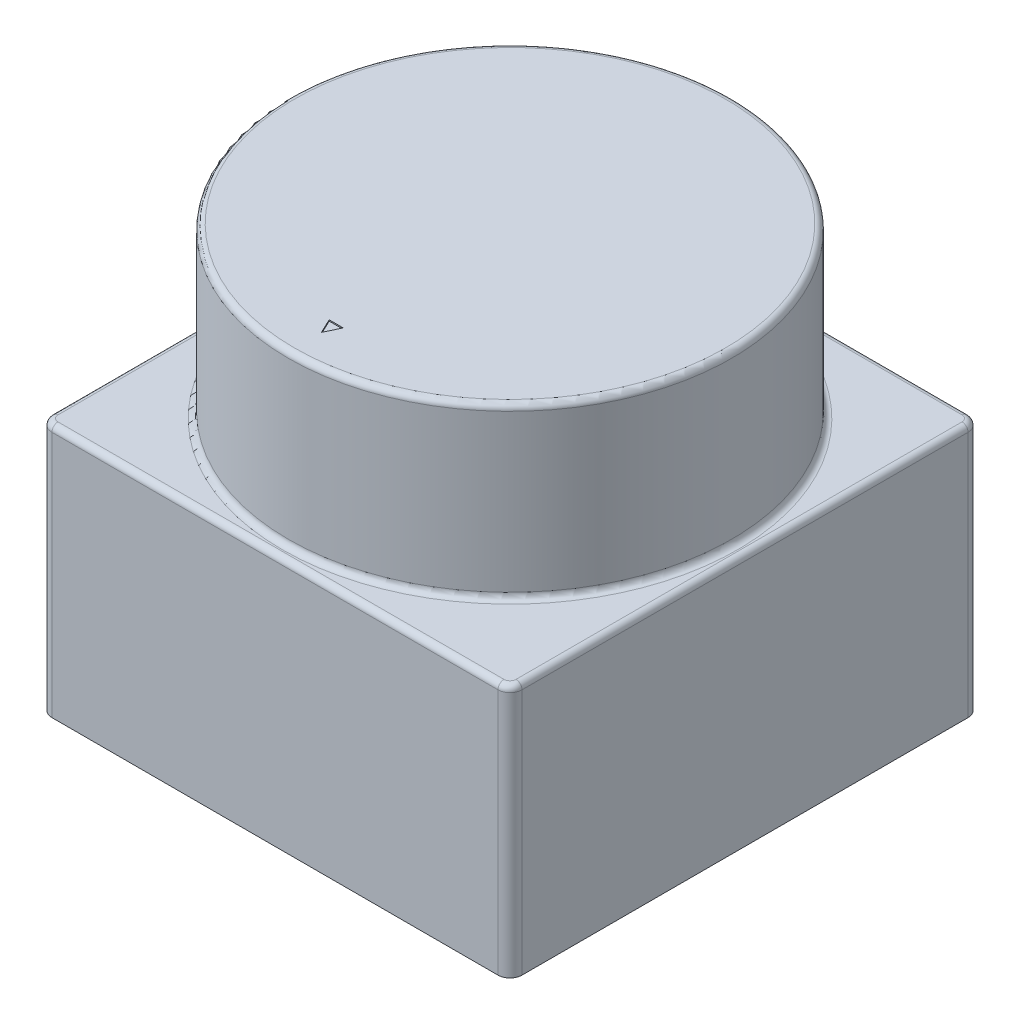
SolidWorks part; units mm, degrees
ref_plane "前视基准面" through (0, 0, 0) normal (0, 0, 1) x (1, 0, 0)
ref_plane "上视基准面" through (0, 0, 0) normal (0, 1, 0) x (1, 0, 0)
ref_plane "右视基准面" through (0, 0, 0) normal (1, 0, 0) x (0, 0, -1)
sketch "草图1" plane through (0, 0, 0) normal (0, 1, 0) x (1, 0, 0)
  line L1 (-19.5, 19.5) -> (19.5, 19.5)
  line L2 (-19.5, 19.5) -> (-19.5, -19.5)
  line L3 (-19.5, -19.5) -> (19.5, -19.5)
  line L4 (19.5, 19.5) -> (19.5, -19.5)
  line L5 (-19.5, 19.5) -> (19.5, -19.5) construction
  line L6 (-19.5, -19.5) -> (19.5, 19.5) construction
  point P0 (0, 0)
  dimension "D1" = 39
extrude "凸台-拉伸1" add sketch "草图1" along normal blind 21
sketch "草图2" plane through (0, 21, 0) normal (0, 1, 0) x (1, 0, 0)
  circle A0 centre (0, 0) radius 18.381
extrude "凸台-拉伸2" add sketch "草图2" along normal blind 14
fillet "圆角1" radius 1 4 edges at (-19.5, 10.5, -19.5) (-19.5, 10.5, 19.5) (19.5, 10.5, 19.5) (19.5, 10.5, -19.5)
fillet "圆角2" radius 0.5 10 edges at (0, 35, 18.381) (19.2071, 21, -19.2071) (19.5, 21, 0) (19.2071, 21, 19.2071) (0, 21, 19.5) (-19.2071, 21, 19.2071) (-19.5, 21, 0) (-19.2071, 21, -19.2071) (0, 21, -19.5) (0, 21, 18.381)
sketch "草图3" plane through (0, 35, 0) normal (0, 1, 0) x (1, 0, 0)
  line L0 (0, -15.6446) -> (-0.5833, -14.4176)
  line L1 (-0.5833, -14.4176) -> (0.5833, -14.4176)
  line L2 (0.5833, -14.4176) -> (0, -15.6446)
  line L3 (0, 0) -> (0, -15.6446) construction
  point P4 (0.7946, -14.1523)
  point P6 (0, -14.4176)
  point P7 (0.5833, -14.4176)
extrude "切除-拉伸1" cut sketch "草图3" against normal blind 0.1
